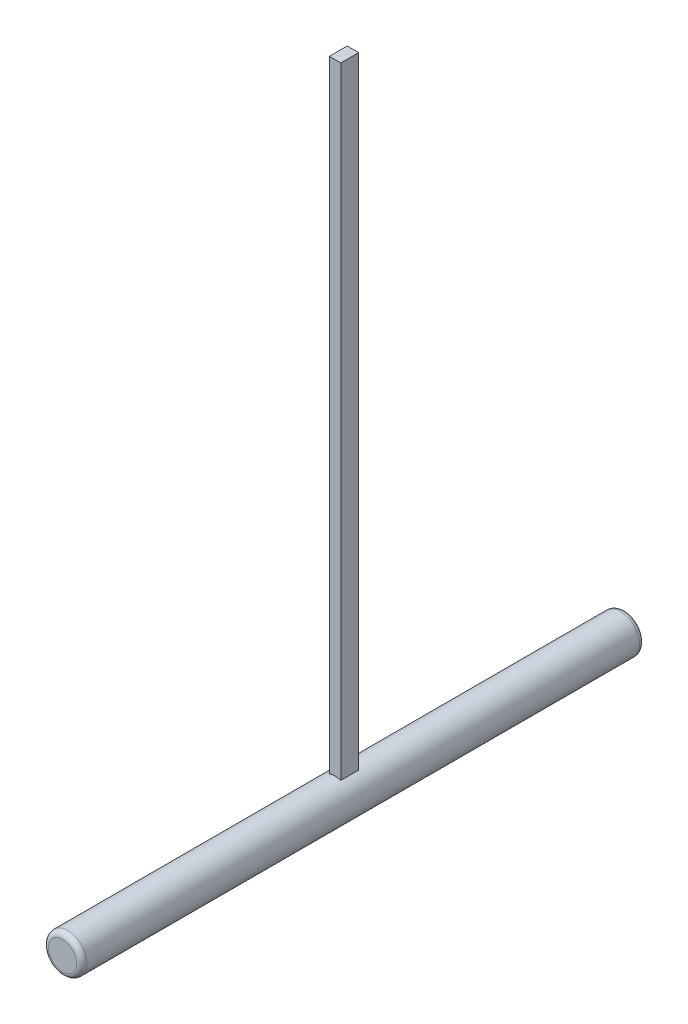
SolidWorks part; units mm, degrees
ref_plane "Front Plane" through (0, 0, 0) normal (0, 0, 1) x (1, 0, 0)
ref_plane "Top Plane" through (0, 0, 0) normal (0, 1, 0) x (1, 0, 0)
ref_plane "Right Plane" through (0, 0, 0) normal (1, 0, 0) x (0, 0, -1)
sketch "Sketch1" plane through (0, 0, 0) normal (0, 0, 1) x (1, 0, 0)
  circle A0 centre (0, 0) radius 7.5
  dimension "D1" = 15
extrude "Boss-Extrude1" add sketch "Sketch1" along normal blind 220
fillet "Fillet1" radius 2 2 edges at (7.5, 0, 0) (7.5, 0, 220)
ref_plane "Plane1" through (0, 250, 0) normal (0, 1, 0) x (1, 0, 0)
sketch "Sketch3" plane through (0, 250, 0) normal (0, 1, 0) x (1, 0, 0)
  line L0 (0, 0) -> (0, -220) construction
  line L1 (-2.245, -106.505) -> (2.245, -106.505)
  line L2 (-2.245, -106.505) -> (-2.245, -113.495)
  line L3 (-2.245, -113.495) -> (2.245, -113.495)
  line L4 (2.245, -106.505) -> (2.245, -113.495)
  line L5 (-2.245, -106.505) -> (2.245, -113.495) construction
  line L6 (-2.245, -113.495) -> (2.245, -106.505) construction
  line L7 (-5.5, -220) -> (5.5, -220) construction
  point P0 (0, -110)
  point P10 (0, 0)
  point P11 (0, 0)
  point P12 (0, 0)
  point P13 (-83.062, -109.6924)
  point P14 (0, -110)
  dimension "D1" = 4.49
  dimension "D2" = 6.99
extrude "Boss-Extrude2" add sketch "Sketch3" against normal up to surface (242.8439 mm away)
